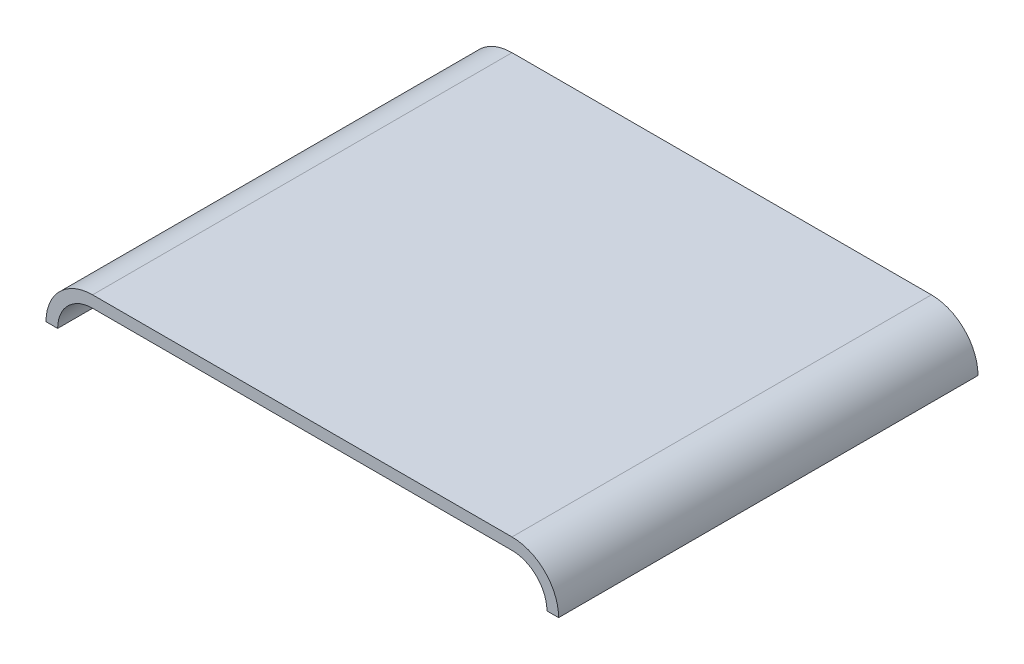
SolidWorks part; units mm, degrees
ref_plane "Front Plane" through (0, 0, 0) normal (0, 0, 1) x (1, 0, 0)
ref_plane "Top Plane" through (0, 0, 0) normal (0, 1, 0) x (1, 0, 0)
ref_plane "Right Plane" through (0, 0, 0) normal (1, 0, 0) x (0, 0, -1)
sketch "Sketch1" plane through (0, 0, 0) normal (0, 0, 1) x (1, 0, 0)
  line L0 (0, 18.4549) -> (0, 0) construction
  line L1 (0, 0) -> (228.6, 0)
  arc A0 (228.6, 0) -> (279.4, -50.8) centre (228.6, -50.8) cw
  dimension "D1" = 50.8
  dimension "D3" = 279.4
extrude "Extrude-Thin1" add sketch "Sketch1" along normal blind 457.2 thin
mirror "Mirror1" about plane through (0, -12.7, 457.2) normal (-1, 0, 0) of "Extrude-Thin1"
sketch "Sketch2" plane through (0, -50.8, 0) normal (0, -1, 0) x (1, 0, 0)
  line L0 (273.05, 0) -> (273.05, 457.2) construction
  line L1 (279.4, 0) -> (266.7, 0) construction
  line L2 (279.4, 457.2) -> (266.7, 457.2) construction
  line L3 (-273.05, 0) -> (-273.05, 457.2) construction
  line L4 (-279.4, 0) -> (-266.7, 0) construction
  line L5 (-279.4, 457.2) -> (-266.7, 457.2) construction
